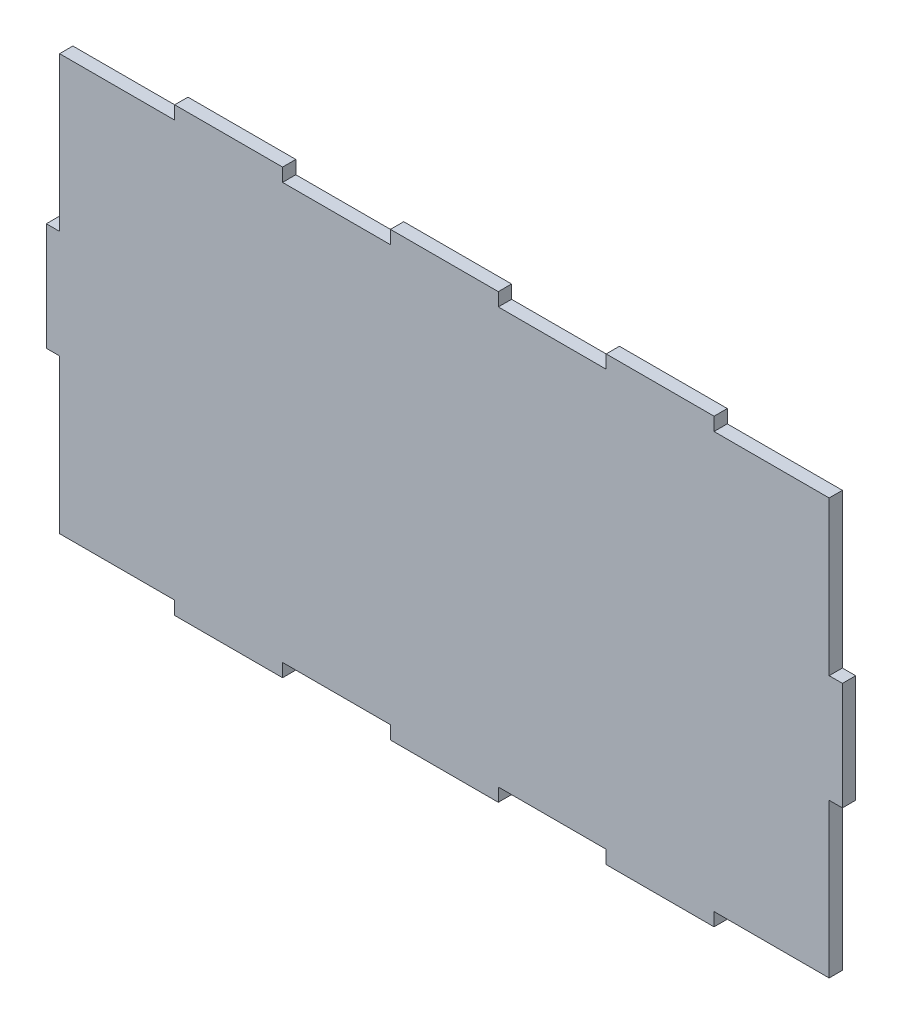
SolidWorks part; units mm, degrees
ref_plane "Alzado" through (0, 0, 0) normal (0, 0, 1) x (1, 0, 0)
ref_plane "Planta" through (0, 0, 0) normal (0, 1, 0) x (1, 0, 0)
ref_plane "Vista lateral" through (0, 0, 0) normal (1, 0, 0) x (0, 0, -1)
sketch "Model" plane through (0, 0, 0) normal (0, 0, 1) x (1, 0, 0)
  line L0 (289, 97) -> (289, 62.195)
  line L1 (289, 62.195) -> (286, 62.195)
  line L2 (286, 62.195) -> (286, 37.805)
  line L3 (286, 37.805) -> (289, 37.805)
  line L4 (289, 37.805) -> (289, 13.415)
  line L5 (289, 13.415) -> (289, 3)
  line L6 (289, 3) -> (315.025, 3)
  line L7 (315.025, 3) -> (315.025, 0)
  line L8 (315.025, 0) -> (339.415, 0)
  line L9 (339.415, 0) -> (339.415, 3)
  line L10 (339.415, 3) -> (363.805, 3)
  line L11 (363.805, 3) -> (363.805, 0)
  line L12 (363.805, 0) -> (388.195, 0)
  line L13 (388.195, 0) -> (388.195, 3)
  line L14 (388.195, 3) -> (412.585, 3)
  line L15 (412.585, 3) -> (412.585, 0)
  line L16 (412.585, 0) -> (436.975, 0)
  line L17 (436.975, 0) -> (436.975, 3)
  line L18 (436.975, 3) -> (461.365, 3)
  line L19 (461.365, 3) -> (463, 3)
  line L20 (463, 3) -> (463, 37.805)
  line L21 (463, 37.805) -> (466, 37.805)
  line L22 (466, 37.805) -> (466, 62.195)
  line L23 (466, 62.195) -> (463, 62.195)
  line L24 (463, 62.195) -> (463, 86.585)
  line L25 (463, 86.585) -> (463, 97)
  line L26 (463, 97) -> (436.975, 97)
  line L27 (436.975, 97) -> (436.975, 100)
  line L28 (436.975, 100) -> (412.585, 100)
  line L29 (412.585, 100) -> (412.585, 97)
  line L30 (412.585, 97) -> (388.195, 97)
  line L31 (388.195, 97) -> (388.195, 100)
  line L32 (388.195, 100) -> (363.805, 100)
  line L33 (363.805, 100) -> (363.805, 97)
  line L34 (363.805, 97) -> (339.415, 97)
  line L35 (339.415, 97) -> (339.415, 100)
  line L36 (339.415, 100) -> (315.025, 100)
  line L37 (315.025, 100) -> (315.025, 97)
  line L38 (315.025, 97) -> (290.635, 97)
  line L39 (290.635, 97) -> (289, 97)
extrude "Saliente-Extruir1" add sketch "Model" along normal blind 3
